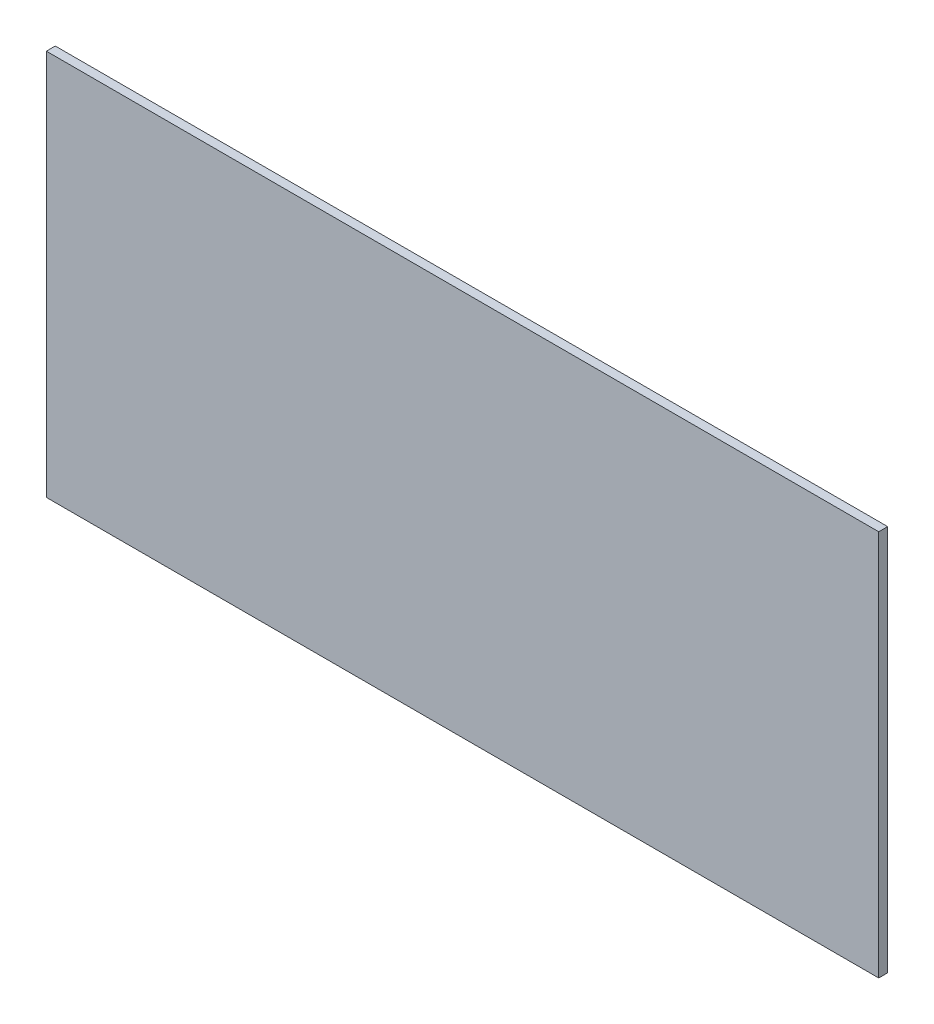
SolidWorks part; units mm, degrees
material "A-Glass Fiber"
ref_plane "Front Plane" through (0, 0, 0) normal (0, 0, 1) x (1, 0, 0)
ref_plane "Top Plane" through (0, 0, 0) normal (0, 1, 0) x (1, 0, 0)
ref_plane "Right Plane" through (0, 0, 0) normal (1, 0, 0) x (0, 0, -1)
sketch "Sketch1" plane through (0, 0, 0) normal (0, 0, 1) x (1, 0, 0)
  line L0 (140, 643.0888) -> (140, 773.0888) construction
  line L1 (-140, 643.0888) -> (140, 643.0888) construction
  line L2 (-140, 773.0888) -> (-140, 643.0888) construction
  line L3 (140, 773.0888) -> (-140, 773.0888) construction
  line L4 (140, 643.0888) -> (140, 773.0888)
  line L5 (-140, 643.0888) -> (140, 643.0888)
  line L6 (-140, 773.0888) -> (-140, 643.0888)
  line L7 (140, 773.0888) -> (-140, 773.0888)
extrude "Boss-Extrude1" add sketch "Sketch1" against normal blind 3
